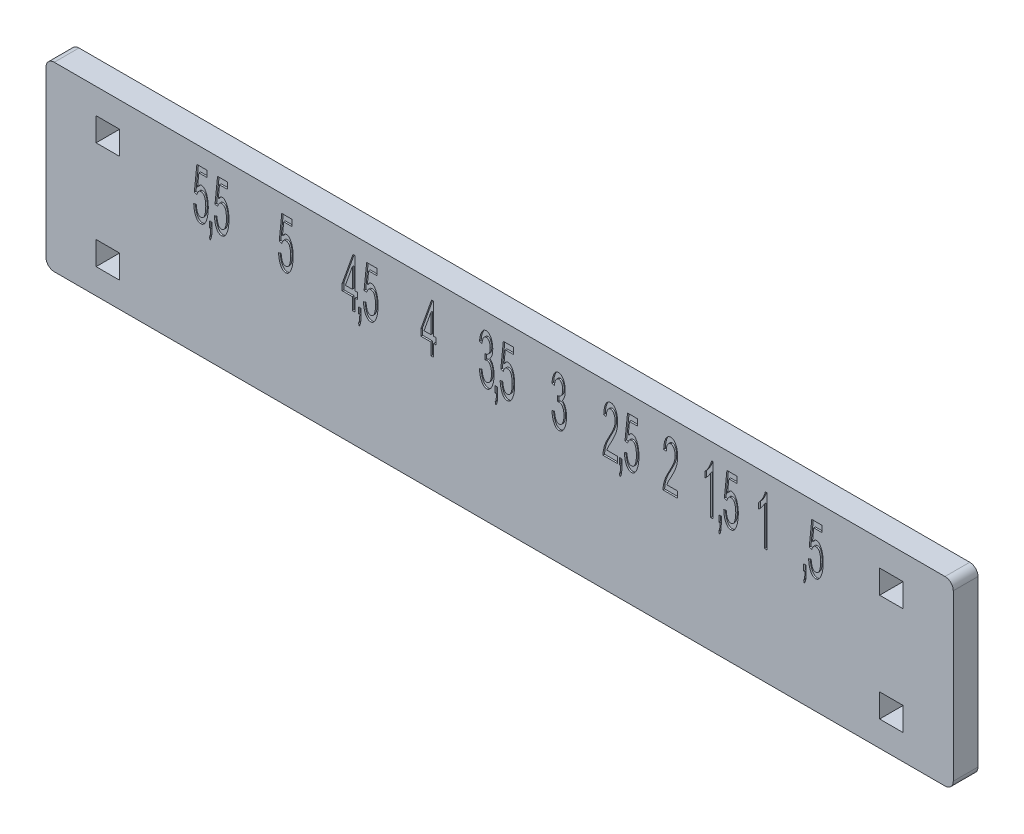
SolidWorks part; units mm, degrees
ref_plane "Спереди" through (0, 0, 0) normal (0, 0, 1) x (1, 0, 0)
ref_plane "Сверху" through (0, 0, 0) normal (0, 1, 0) x (1, 0, 0)
ref_plane "Справа" through (0, 0, 0) normal (1, 0, 0) x (0, 0, -1)
sketch "Эскиз2" plane through (0, 0, 0) normal (0, 0, 1) x (1, 0, 0)
  line L0 (-15.9107, 0) -> (16.719, 0) construction
  line L1 (-55, 11) -> (55, 11)
  line L2 (-55, 11) -> (-55, -11)
  line L3 (-55, -11) -> (55, -11)
  line L4 (55, 11) -> (55, -11)
  line L5 (-55, 11) -> (55, -11) construction
  line L6 (-55, -11) -> (55, 11) construction
  line L11 (-48.925, -5.075) -> (-46.075, -7.925) construction
  line L12 (-48.925, -7.925) -> (-46.075, -5.075) construction
  line L13 (-46.075, -7.925) -> (-46.075, -5.075)
  line L14 (-48.925, -5.075) -> (-46.075, -5.075)
  line L19 (-35.25, -19.9206) -> (35.25, -19.9206) construction
  line L20 (-48.925, -7.925) -> (-48.925, -5.075)
  line L21 (-48.925, 7.925) -> (-46.075, 7.925)
  line L22 (-48.925, 7.925) -> (-48.925, 5.075)
  line L23 (-48.925, 5.075) -> (-46.075, 5.075)
  line L24 (-46.075, 7.925) -> (-46.075, 5.075)
  line L25 (-48.925, 7.925) -> (-46.075, 5.075) construction
  line L26 (-48.925, 5.075) -> (-46.075, 7.925) construction
  line L27 (-48.925, -7.925) -> (-46.075, -7.925)
  line L28 (0, 0) -> (0, 20.7293) construction
  line L29 (46.075, -7.925) -> (46.075, -5.075)
  line L30 (48.925, -7.925) -> (46.075, -5.075) construction
  line L31 (48.925, -5.075) -> (46.075, -7.925) construction
  line L32 (48.925, -7.925) -> (46.075, -7.925)
  line L33 (48.925, -7.925) -> (48.925, -5.075)
  line L34 (48.925, -5.075) -> (46.075, -5.075)
  line L35 (48.925, 5.075) -> (46.075, 7.925) construction
  line L36 (48.925, 7.925) -> (46.075, 5.075) construction
  line L37 (46.075, 7.925) -> (46.075, 5.075)
  line L38 (48.925, 5.075) -> (46.075, 5.075)
  line L39 (48.925, 7.925) -> (48.925, 5.075)
  line L40 (48.925, 7.925) -> (46.075, 7.925)
  point P0 (0, 0)
  point P14 (-47.5, -6.5)
  point P20 (0, -19.9206)
  point P21 (-47.5, 6.5)
  point P31 (47.5, 6.5)
  dimension "D1" = 22
  dimension "D2" = 7.5
  dimension "D3" = 4.5
  dimension "D4" = 110
  dimension "D6" = 70.5
  dimension "D7" = 2.85
extrude "Бобышка-Вытянуть1" add sketch "Эскиз2" along normal blind 3
fillet "Скругление1" radius 1 4 edges at (-55, -11, 1.5) (-55, 11, 1.5) (55, -11, 1.5) (55, 11, 1.5)
sketch "Эскиз3" [suppressed] plane through (0, 0, 3) normal (0, 0, 1) x (1, 0, 0)
  line L0 (-31, 0.6827) -> (-17, 0.6827) construction
  line L1 (-17, 0.6827) -> (-3, 0.6827) construction
  line L2 (-3, 0.6827) -> (11, 0.6827) construction
  line L3 (11, 0.6827) -> (25, 0.6827) construction
  line L4 (-3, 0.6827) -> (0, 0.6827) construction
  line L5 (-38.25, -4.6945) -> (-24.15, -4.6945) construction
  line L6 (-24.15, -4.6945) -> (-10.05, -4.6945) construction
  line L7 (-10.05, -4.6945) -> (4.05, -4.6945) construction
  line L8 (4.05, -4.6945) -> (18.15, -4.6945) construction
  line L9 (18.15, -4.6945) -> (32.25, -4.6945) construction
  line L10 (-3, -4.6945) -> (0, -4.6945) construction
  text T0 "12\r\n"
  text T1 "11\r\n"
  text T2 "10\r\n"
  text T3 "9,5\r\n"
  text T4 "9\r\n"
  text T5 "8,5\r\n"
  text T6 "8\r\n"
  text T7 "7,5\r\n"
  text T8 "7\r\n\r\n"
  text T9 "6,5\r\n"
  text T10 "6\r\n"
  dimension "D1" = 56
  dimension "D2" = 3
  dimension "D3" = 70.5
  dimension "D4" = 3
sketch "Эскиз4" plane through (0, 0, 3) normal (0, 0, 1) x (1, 0, 0)
  line L12 (55, 10) -> (55, -10) construction
  line L13 (-38, 3) -> (-32.3, 3) construction
  line L18 (-32.3, 3) -> (-28.22, 3) construction
  line L19 (-28.22, 3) -> (-23.02, 3) construction
  line L24 (-23.02, 3) -> (-18.94, 3) construction
  line L25 (-18.94, 3) -> (-14.24, 3) construction
  line L26 (-14.24, 3) -> (-10.16, 3) construction
  line L27 (-10.16, 3) -> (-5.96, 3) construction
  line L32 (-5.96, 3) -> (-1.88, 3) construction
  line L33 (-1.88, 3) -> (1.82, 3) construction
  line L34 (1.82, 3) -> (5.9, 3) construction
  line L35 (5.9, 3) -> (9.1, 3) construction
  line L36 (-54, 11) -> (54, 11) construction
  line L44 (9.1, 3) -> (13.18, 3) construction
  line L46 (13.18, 3) -> (15.88, 3) construction
  line L48 (15.88, 3) -> (19.96, 3) construction
  line L54 (19.96, 3) -> (22.16, 3) construction
  line L55 (22.16, 3) -> (26.24, 3) construction
  line L56 (26.24, 3) -> (27.94, 3) construction
  line L57 (27.94, 3) -> (32.02, 3) construction
  line L58 (32.02, 3) -> (33.22, 3) construction
  line L59 (33.22, 3) -> (37.3, 3) construction
  line L60 (37.3, 3) -> (38, 3) construction
  line L61 (-55, 10) -> (-55, -10) construction
  circle A19 centre (-35.15, 3) radius 2.85 construction
  circle A20 centre (-25.62, 3) radius 2.6 construction
  circle A21 centre (-16.59, 3) radius 2.35 construction
  circle A22 centre (-8.06, 3) radius 2.1 construction
  circle A23 centre (-0.03, 3) radius 1.85 construction
  circle A24 centre (7.5, 3) radius 1.6 construction
  circle A25 centre (14.53, 3) radius 1.35 construction
  circle A26 centre (21.06, 3) radius 1.1 construction
  circle A27 centre (27.09, 3) radius 0.85 construction
  circle A28 centre (32.62, 3) radius 0.6 construction
  circle A29 centre (37.65, 3) radius 0.35 construction
  text T0 " 5,5        5        4,5       4       3,5      3      2,5    2    1,5   1     ,5" font "Arial" height 6
  dimension "D10" = 1.2
  dimension "D11" = 0.7
  dimension "D12" = 17
  dimension "D13" = 17
  dimension "D14" = 8
  dimension "D2" = 5.2
  dimension "D3" = 4.7
  dimension "D4" = 4.2
  dimension "D5" = 3.7
  dimension "D6" = 3.2
  dimension "D1" = 5.7
  dimension "D7" = 2.7
  dimension "D8" = 2.2
  dimension "D9" = 1.7
extrude "Вырез-Вытянуть1" cut sketch "Эскиз4" against normal blind 0.2
